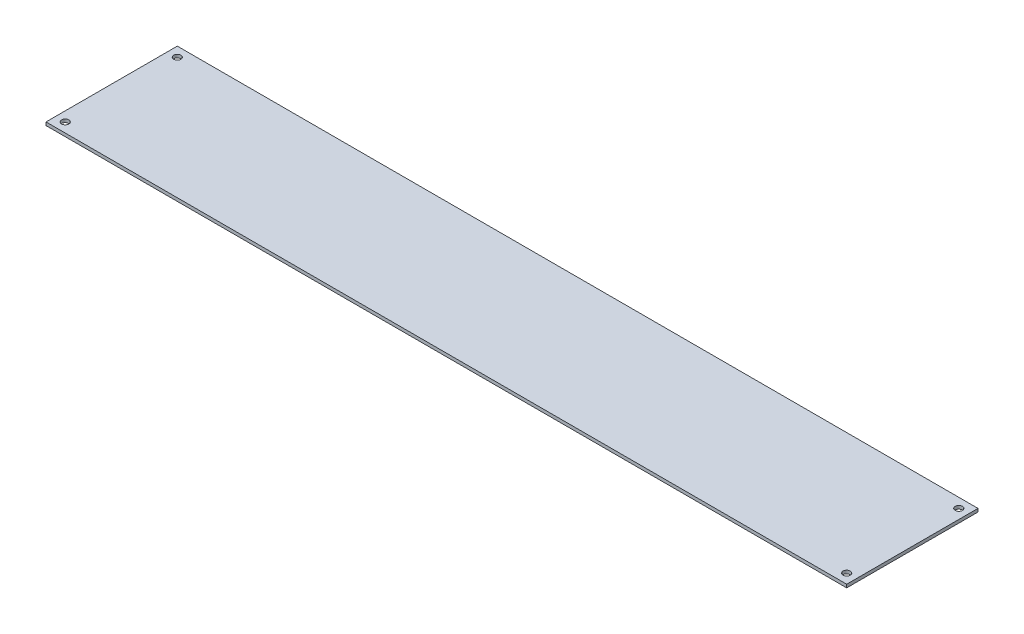
SolidWorks part; units mm, degrees
ref_plane "Front Plane" through (0, 0, 0) normal (0, 0, 1) x (1, 0, 0)
ref_plane "Top Plane" through (0, 0, 0) normal (0, 1, 0) x (1, 0, 0)
ref_plane "Right Plane" through (0, 0, 0) normal (1, 0, 0) x (0, 0, -1)
sketch "Sketch1" plane through (0, 0, 0) normal (0, 1, 0) x (1, 0, 0)
  line L1 (0, 0) -> (500, 0)
  line L2 (0, 0) -> (0, 82)
  line L3 (0, 82) -> (500, 82)
  line L4 (500, 0) -> (500, 82)
  dimension "D1" = 500
  dimension "D2" = 82
extrude "Boss-Extrude1" add sketch "Sketch1" along normal blind 2
hole_wizard "M4 Clearance Hole1" positions "Sketch3" profile "Sketch4" hole size "M4" standard "DIN" end condition up to next
sketch "Sketch3" plane through (0, 0, 0) normal (0, -1, 0) x (-1, 0, 0)
  line L0 (-500, 82) -> (0, 82) construction
  line L1 (0, 82) -> (0, 0) construction
  line L2 (-500, 0) -> (-500, 82) construction
  line L3 (0, 0) -> (-500, 0) construction
  point P0 (-6, 6)
  point P2 (-6, 76)
  point P4 (-494, 76)
  point P6 (-494, 6)
  dimension "D1" = 6
  dimension "D2" = 6
  dimension "D3" = 6
  dimension "D4" = 6
sketch "Sketch4" plane through (6, 0, -6) normal (1, 0, 0) x (0, 0, -1)
  line L0 (0, 0) -> (0, 2)
  line L1 (0, 2) -> (2.25, 2)
  line L2 (2.25, 2) -> (2.25, 0)
  line L5 (2.25, 0) -> (0, 0)
  line L11 (0, -6.35) -> (0, 107.95) construction
  dimension "Thru Hole Dia." = 4.5
  dimension "Thru Hole Depth" = 2
sketch "Sketch5" plane through (0, 0, 0) normal (0, -1, 0) x (1, 0, 0)
  line L0 (0, -82) -> (0, 0) construction
  line L1 (500, -82) -> (0, -82) construction
  line L189 (0, 0) -> (500, 0) construction
  line L190 (26.3868, -5) -> (24.9434, -2.5)
  line L191 (24.9434, -2.5) -> (22.0566, -2.5)
  line L192 (22.0566, -2.5) -> (20.6132, -5)
  line L193 (20.6132, -5) -> (22.0566, -7.5)
  line L194 (22.0566, -7.5) -> (24.9434, -7.5)
  line L195 (24.9434, -7.5) -> (26.3868, -5)
  line L196 (36.3868, -5) -> (34.9434, -2.5)
  line L197 (34.9434, -2.5) -> (32.0566, -2.5)
  line L198 (32.0566, -2.5) -> (30.6132, -5)
  line L199 (30.6132, -5) -> (32.0566, -7.5)
  line L200 (32.0566, -7.5) -> (34.9434, -7.5)
  line L201 (34.9434, -7.5) -> (36.3868, -5)
  line L202 (46.3868, -5) -> (44.9434, -2.5)
  line L203 (44.9434, -2.5) -> (42.0566, -2.5)
  line L204 (42.0566, -2.5) -> (40.6132, -5)
  line L205 (40.6132, -5) -> (42.0566, -7.5)
  line L206 (42.0566, -7.5) -> (44.9434, -7.5)
  line L207 (44.9434, -7.5) -> (46.3868, -5)
  line L208 (56.3868, -5) -> (54.9434, -2.5)
  line L209 (54.9434, -2.5) -> (52.0566, -2.5)
  line L210 (52.0566, -2.5) -> (50.6132, -5)
  line L211 (50.6132, -5) -> (52.0566, -7.5)
  line L212 (52.0566, -7.5) -> (54.9434, -7.5)
  line L213 (54.9434, -7.5) -> (56.3868, -5)
  line L214 (66.3868, -5) -> (64.9434, -2.5)
  line L215 (64.9434, -2.5) -> (62.0566, -2.5)
  line L216 (62.0566, -2.5) -> (60.6132, -5)
  line L217 (60.6132, -5) -> (62.0566, -7.5)
  line L218 (62.0566, -7.5) -> (64.9434, -7.5)
  line L219 (64.9434, -7.5) -> (66.3868, -5)
  line L220 (76.3868, -5) -> (74.9434, -2.5)
  line L221 (74.9434, -2.5) -> (72.0566, -2.5)
  line L222 (72.0566, -2.5) -> (70.6132, -5)
  line L223 (70.6132, -5) -> (72.0566, -7.5)
  line L224 (72.0566, -7.5) -> (74.9434, -7.5)
  line L225 (74.9434, -7.5) -> (76.3868, -5)
  line L226 (86.3868, -5) -> (84.9434, -2.5)
  line L227 (84.9434, -2.5) -> (82.0566, -2.5)
  line L228 (82.0566, -2.5) -> (80.6132, -5)
  line L229 (80.6132, -5) -> (82.0566, -7.5)
  line L230 (82.0566, -7.5) -> (84.9434, -7.5)
  line L231 (84.9434, -7.5) -> (86.3868, -5)
  line L232 (96.3868, -5) -> (94.9434, -2.5)
  line L233 (94.9434, -2.5) -> (92.0566, -2.5)
  line L234 (92.0566, -2.5) -> (90.6132, -5)
  line L235 (90.6132, -5) -> (92.0566, -7.5)
  line L236 (92.0566, -7.5) -> (94.9434, -7.5)
  line L237 (94.9434, -7.5) -> (96.3868, -5)
  line L238 (106.3868, -5) -> (104.9434, -2.5)
  line L239 (104.9434, -2.5) -> (102.0566, -2.5)
  line L240 (102.0566, -2.5) -> (100.6132, -5)
  line L241 (100.6132, -5) -> (102.0566, -7.5)
  line L242 (102.0566, -7.5) -> (104.9434, -7.5)
  line L243 (104.9434, -7.5) -> (106.3868, -5)
  line L244 (116.3868, -5) -> (114.9434, -2.5)
  line L245 (114.9434, -2.5) -> (112.0566, -2.5)
  line L246 (112.0566, -2.5) -> (110.6132, -5)
  line L247 (110.6132, -5) -> (112.0566, -7.5)
  line L248 (112.0566, -7.5) -> (114.9434, -7.5)
  line L249 (114.9434, -7.5) -> (116.3868, -5)
  line L250 (126.3868, -5) -> (124.9434, -2.5)
  line L251 (124.9434, -2.5) -> (122.0566, -2.5)
  line L252 (122.0566, -2.5) -> (120.6132, -5)
  line L253 (120.6132, -5) -> (122.0566, -7.5)
  line L254 (122.0566, -7.5) -> (124.9434, -7.5)
  line L255 (124.9434, -7.5) -> (126.3868, -5)
  line L256 (136.3868, -5) -> (134.9434, -2.5)
  line L257 (134.9434, -2.5) -> (132.0566, -2.5)
  line L258 (132.0566, -2.5) -> (130.6132, -5)
  line L259 (130.6132, -5) -> (132.0566, -7.5)
  line L260 (132.0566, -7.5) -> (134.9434, -7.5)
  line L261 (134.9434, -7.5) -> (136.3868, -5)
  line L262 (146.3868, -5) -> (144.9434, -2.5)
  line L263 (144.9434, -2.5) -> (142.0566, -2.5)
  line L264 (142.0566, -2.5) -> (140.6132, -5)
  line L265 (140.6132, -5) -> (142.0566, -7.5)
  line L266 (142.0566, -7.5) -> (144.9434, -7.5)
  line L267 (144.9434, -7.5) -> (146.3868, -5)
  line L268 (36.3868, -15) -> (34.9434, -12.5)
  line L269 (34.9434, -12.5) -> (32.0566, -12.5)
  line L270 (32.0566, -12.5) -> (30.6132, -15)
  line L271 (30.6132, -15) -> (32.0566, -17.5)
  line L272 (32.0566, -17.5) -> (34.9434, -17.5)
  line L273 (34.9434, -17.5) -> (36.3868, -15)
  line L274 (46.3868, -15) -> (44.9434, -12.5)
  line L275 (44.9434, -12.5) -> (42.0566, -12.5)
  line L276 (42.0566, -12.5) -> (40.6132, -15)
  line L277 (40.6132, -15) -> (42.0566, -17.5)
  line L278 (42.0566, -17.5) -> (44.9434, -17.5)
  line L279 (44.9434, -17.5) -> (46.3868, -15)
  line L280 (56.3868, -15) -> (54.9434, -12.5)
  line L281 (54.9434, -12.5) -> (52.0566, -12.5)
  line L282 (52.0566, -12.5) -> (50.6132, -15)
  line L283 (50.6132, -15) -> (52.0566, -17.5)
  line L284 (52.0566, -17.5) -> (54.9434, -17.5)
  line L285 (54.9434, -17.5) -> (56.3868, -15)
  line L286 (66.3868, -15) -> (64.9434, -12.5)
  line L287 (64.9434, -12.5) -> (62.0566, -12.5)
  line L288 (62.0566, -12.5) -> (60.6132, -15)
  line L289 (60.6132, -15) -> (62.0566, -17.5)
  line L290 (62.0566, -17.5) -> (64.9434, -17.5)
  line L291 (64.9434, -17.5) -> (66.3868, -15)
  line L292 (76.3868, -15) -> (74.9434, -12.5)
  line L293 (74.9434, -12.5) -> (72.0566, -12.5)
  line L294 (72.0566, -12.5) -> (70.6132, -15)
  line L295 (70.6132, -15) -> (72.0566, -17.5)
  line L296 (72.0566, -17.5) -> (74.9434, -17.5)
  line L297 (74.9434, -17.5) -> (76.3868, -15)
  line L298 (86.3868, -15) -> (84.9434, -12.5)
  line L299 (84.9434, -12.5) -> (82.0566, -12.5)
  line L300 (82.0566, -12.5) -> (80.6132, -15)
  line L301 (80.6132, -15) -> (82.0566, -17.5)
  line L302 (82.0566, -17.5) -> (84.9434, -17.5)
  line L303 (84.9434, -17.5) -> (86.3868, -15)
  line L304 (96.3868, -15) -> (94.9434, -12.5)
  line L305 (94.9434, -12.5) -> (92.0566, -12.5)
  line L306 (92.0566, -12.5) -> (90.6132, -15)
  line L307 (90.6132, -15) -> (92.0566, -17.5)
  line L308 (92.0566, -17.5) -> (94.9434, -17.5)
  line L309 (94.9434, -17.5) -> (96.3868, -15)
  line L310 (106.3868, -15) -> (104.9434, -12.5)
  line L311 (104.9434, -12.5) -> (102.0566, -12.5)
  line L312 (102.0566, -12.5) -> (100.6132, -15)
  line L313 (100.6132, -15) -> (102.0566, -17.5)
  line L314 (102.0566, -17.5) -> (104.9434, -17.5)
  line L315 (104.9434, -17.5) -> (106.3868, -15)
  line L316 (116.3868, -15) -> (114.9434, -12.5)
  line L317 (114.9434, -12.5) -> (112.0566, -12.5)
  line L318 (112.0566, -12.5) -> (110.6132, -15)
  line L319 (110.6132, -15) -> (112.0566, -17.5)
  line L320 (112.0566, -17.5) -> (114.9434, -17.5)
  line L321 (114.9434, -17.5) -> (116.3868, -15)
  line L322 (126.3868, -15) -> (124.9434, -12.5)
  line L323 (124.9434, -12.5) -> (122.0566, -12.5)
  line L324 (122.0566, -12.5) -> (120.6132, -15)
  line L325 (120.6132, -15) -> (122.0566, -17.5)
  line L326 (122.0566, -17.5) -> (124.9434, -17.5)
  line L327 (124.9434, -17.5) -> (126.3868, -15)
  line L328 (136.3868, -15) -> (134.9434, -12.5)
  line L329 (134.9434, -12.5) -> (132.0566, -12.5)
  line L330 (132.0566, -12.5) -> (130.6132, -15)
  line L331 (130.6132, -15) -> (132.0566, -17.5)
  line L332 (132.0566, -17.5) -> (134.9434, -17.5)
  line L333 (134.9434, -17.5) -> (136.3868, -15)
  line L334 (146.3868, -15) -> (144.9434, -12.5)
  line L335 (144.9434, -12.5) -> (142.0566, -12.5)
  line L336 (142.0566, -12.5) -> (140.6132, -15)
  line L337 (140.6132, -15) -> (142.0566, -17.5)
  line L338 (142.0566, -17.5) -> (144.9434, -17.5)
  line L339 (144.9434, -17.5) -> (146.3868, -15)
  line L340 (36.3868, -25) -> (34.9434, -22.5)
  line L341 (34.9434, -22.5) -> (32.0566, -22.5)
  line L342 (32.0566, -22.5) -> (30.6132, -25)
  line L343 (30.6132, -25) -> (32.0566, -27.5)
  line L344 (32.0566, -27.5) -> (34.9434, -27.5)
  line L345 (34.9434, -27.5) -> (36.3868, -25)
  line L346 (46.3868, -25) -> (44.9434, -22.5)
  line L347 (44.9434, -22.5) -> (42.0566, -22.5)
  line L348 (42.0566, -22.5) -> (40.6132, -25)
  line L349 (40.6132, -25) -> (42.0566, -27.5)
  line L350 (42.0566, -27.5) -> (44.9434, -27.5)
  line L351 (44.9434, -27.5) -> (46.3868, -25)
  line L352 (56.3868, -25) -> (54.9434, -22.5)
  line L353 (54.9434, -22.5) -> (52.0566, -22.5)
  line L354 (52.0566, -22.5) -> (50.6132, -25)
  line L355 (50.6132, -25) -> (52.0566, -27.5)
  line L356 (52.0566, -27.5) -> (54.9434, -27.5)
  line L357 (54.9434, -27.5) -> (56.3868, -25)
  line L358 (66.3868, -25) -> (64.9434, -22.5)
  line L359 (64.9434, -22.5) -> (62.0566, -22.5)
  line L360 (62.0566, -22.5) -> (60.6132, -25)
  line L361 (60.6132, -25) -> (62.0566, -27.5)
  line L362 (62.0566, -27.5) -> (64.9434, -27.5)
  line L363 (64.9434, -27.5) -> (66.3868, -25)
  line L364 (76.3868, -25) -> (74.9434, -22.5)
  line L365 (74.9434, -22.5) -> (72.0566, -22.5)
  line L366 (72.0566, -22.5) -> (70.6132, -25)
  line L367 (70.6132, -25) -> (72.0566, -27.5)
  line L368 (72.0566, -27.5) -> (74.9434, -27.5)
  line L369 (74.9434, -27.5) -> (76.3868, -25)
  line L370 (86.3868, -25) -> (84.9434, -22.5)
  line L371 (84.9434, -22.5) -> (82.0566, -22.5)
  line L372 (82.0566, -22.5) -> (80.6132, -25)
  line L373 (80.6132, -25) -> (82.0566, -27.5)
  line L374 (82.0566, -27.5) -> (84.9434, -27.5)
  line L375 (84.9434, -27.5) -> (86.3868, -25)
  line L376 (96.3868, -25) -> (94.9434, -22.5)
  line L377 (94.9434, -22.5) -> (92.0566, -22.5)
  line L378 (92.0566, -22.5) -> (90.6132, -25)
  line L379 (90.6132, -25) -> (92.0566, -27.5)
  line L380 (92.0566, -27.5) -> (94.9434, -27.5)
  line L381 (94.9434, -27.5) -> (96.3868, -25)
  line L382 (106.3868, -25) -> (104.9434, -22.5)
  line L383 (104.9434, -22.5) -> (102.0566, -22.5)
  line L384 (102.0566, -22.5) -> (100.6132, -25)
  line L385 (100.6132, -25) -> (102.0566, -27.5)
  line L386 (102.0566, -27.5) -> (104.9434, -27.5)
  line L387 (104.9434, -27.5) -> (106.3868, -25)
  line L388 (116.3868, -25) -> (114.9434, -22.5)
  line L389 (114.9434, -22.5) -> (112.0566, -22.5)
  line L390 (112.0566, -22.5) -> (110.6132, -25)
  line L391 (110.6132, -25) -> (112.0566, -27.5)
  line L392 (112.0566, -27.5) -> (114.9434, -27.5)
  line L393 (114.9434, -27.5) -> (116.3868, -25)
  line L394 (126.3868, -25) -> (124.9434, -22.5)
  line L395 (124.9434, -22.5) -> (122.0566, -22.5)
  line L396 (122.0566, -22.5) -> (120.6132, -25)
  line L397 (120.6132, -25) -> (122.0566, -27.5)
  line L398 (122.0566, -27.5) -> (124.9434, -27.5)
  line L399 (124.9434, -27.5) -> (126.3868, -25)
  line L400 (136.3868, -25) -> (134.9434, -22.5)
  line L401 (134.9434, -22.5) -> (132.0566, -22.5)
  line L402 (132.0566, -22.5) -> (130.6132, -25)
  line L403 (130.6132, -25) -> (132.0566, -27.5)
  line L404 (132.0566, -27.5) -> (134.9434, -27.5)
  line L405 (134.9434, -27.5) -> (136.3868, -25)
  line L412 (36.3868, -35) -> (34.9434, -32.5)
  line L413 (34.9434, -32.5) -> (32.0566, -32.5)
  line L414 (32.0566, -32.5) -> (30.6132, -35)
  line L415 (30.6132, -35) -> (32.0566, -37.5)
  line L416 (32.0566, -37.5) -> (34.9434, -37.5)
  line L417 (34.9434, -37.5) -> (36.3868, -35)
  line L418 (46.3868, -35) -> (44.9434, -32.5)
  line L419 (44.9434, -32.5) -> (42.0566, -32.5)
  line L420 (42.0566, -32.5) -> (40.6132, -35)
  line L421 (40.6132, -35) -> (42.0566, -37.5)
  line L422 (42.0566, -37.5) -> (44.9434, -37.5)
  line L423 (44.9434, -37.5) -> (46.3868, -35)
  line L424 (56.3868, -35) -> (54.9434, -32.5)
  line L425 (54.9434, -32.5) -> (52.0566, -32.5)
  line L426 (52.0566, -32.5) -> (50.6132, -35)
  line L427 (50.6132, -35) -> (52.0566, -37.5)
  line L428 (52.0566, -37.5) -> (54.9434, -37.5)
  line L429 (54.9434, -37.5) -> (56.3868, -35)
  line L430 (66.3868, -35) -> (64.9434, -32.5)
  line L431 (64.9434, -32.5) -> (62.0566, -32.5)
  line L432 (62.0566, -32.5) -> (60.6132, -35)
  line L433 (60.6132, -35) -> (62.0566, -37.5)
  line L434 (62.0566, -37.5) -> (64.9434, -37.5)
  line L435 (64.9434, -37.5) -> (66.3868, -35)
  line L436 (76.3868, -35) -> (74.9434, -32.5)
  line L437 (74.9434, -32.5) -> (72.0566, -32.5)
  line L438 (72.0566, -32.5) -> (70.6132, -35)
  line L439 (70.6132, -35) -> (72.0566, -37.5)
  line L440 (72.0566, -37.5) -> (74.9434, -37.5)
  line L441 (74.9434, -37.5) -> (76.3868, -35)
  line L442 (86.3868, -35) -> (84.9434, -32.5)
  line L443 (84.9434, -32.5) -> (82.0566, -32.5)
  line L444 (82.0566, -32.5) -> (80.6132, -35)
  line L445 (80.6132, -35) -> (82.0566, -37.5)
  line L446 (82.0566, -37.5) -> (84.9434, -37.5)
  line L447 (84.9434, -37.5) -> (86.3868, -35)
  line L448 (96.3868, -35) -> (94.9434, -32.5)
  line L449 (94.9434, -32.5) -> (92.0566, -32.5)
  line L450 (92.0566, -32.5) -> (90.6132, -35)
  line L451 (90.6132, -35) -> (92.0566, -37.5)
  line L452 (92.0566, -37.5) -> (94.9434, -37.5)
  line L453 (94.9434, -37.5) -> (96.3868, -35)
  line L454 (106.3868, -35) -> (104.9434, -32.5)
  line L455 (104.9434, -32.5) -> (102.0566, -32.5)
  line L456 (102.0566, -32.5) -> (100.6132, -35)
  line L457 (100.6132, -35) -> (102.0566, -37.5)
  line L458 (102.0566, -37.5) -> (104.9434, -37.5)
  line L459 (104.9434, -37.5) -> (106.3868, -35)
  line L460 (116.3868, -35) -> (114.9434, -32.5)
  line L461 (114.9434, -32.5) -> (112.0566, -32.5)
  line L462 (112.0566, -32.5) -> (110.6132, -35)
  line L463 (110.6132, -35) -> (112.0566, -37.5)
  line L464 (112.0566, -37.5) -> (114.9434, -37.5)
  line L465 (114.9434, -37.5) -> (116.3868, -35)
  line L466 (126.3868, -35) -> (124.9434, -32.5)
  line L467 (124.9434, -32.5) -> (122.0566, -32.5)
  line L468 (122.0566, -32.5) -> (120.6132, -35)
  line L469 (120.6132, -35) -> (122.0566, -37.5)
  line L470 (122.0566, -37.5) -> (124.9434, -37.5)
  line L471 (124.9434, -37.5) -> (126.3868, -35)
  line L472 (136.3868, -35) -> (134.9434, -32.5)
  line L473 (134.9434, -32.5) -> (132.0566, -32.5)
  line L474 (132.0566, -32.5) -> (130.6132, -35)
  line L475 (130.6132, -35) -> (132.0566, -37.5)
  line L476 (132.0566, -37.5) -> (134.9434, -37.5)
  line L477 (134.9434, -37.5) -> (136.3868, -35)
  line L490 (46.3868, -45) -> (44.9434, -42.5)
  line L491 (44.9434, -42.5) -> (42.0566, -42.5)
  line L492 (42.0566, -42.5) -> (40.6132, -45)
  line L493 (40.6132, -45) -> (42.0566, -47.5)
  line L494 (42.0566, -47.5) -> (44.9434, -47.5)
  line L495 (44.9434, -47.5) -> (46.3868, -45)
  line L496 (56.3868, -45) -> (54.9434, -42.5)
  line L497 (54.9434, -42.5) -> (52.0566, -42.5)
  line L498 (52.0566, -42.5) -> (50.6132, -45)
  line L499 (50.6132, -45) -> (52.0566, -47.5)
  line L500 (52.0566, -47.5) -> (54.9434, -47.5)
  line L501 (54.9434, -47.5) -> (56.3868, -45)
  line L502 (66.3868, -45) -> (64.9434, -42.5)
  line L503 (64.9434, -42.5) -> (62.0566, -42.5)
  line L504 (62.0566, -42.5) -> (60.6132, -45)
  line L505 (60.6132, -45) -> (62.0566, -47.5)
  line L506 (62.0566, -47.5) -> (64.9434, -47.5)
  line L507 (64.9434, -47.5) -> (66.3868, -45)
  line L508 (76.3868, -45) -> (74.9434, -42.5)
  line L509 (74.9434, -42.5) -> (72.0566, -42.5)
  line L510 (72.0566, -42.5) -> (70.6132, -45)
  line L511 (70.6132, -45) -> (72.0566, -47.5)
  line L512 (72.0566, -47.5) -> (74.9434, -47.5)
  line L513 (74.9434, -47.5) -> (76.3868, -45)
  line L514 (86.3868, -45) -> (84.9434, -42.5)
  line L515 (84.9434, -42.5) -> (82.0566, -42.5)
  line L516 (82.0566, -42.5) -> (80.6132, -45)
  line L517 (80.6132, -45) -> (82.0566, -47.5)
  line L518 (82.0566, -47.5) -> (84.9434, -47.5)
  line L519 (84.9434, -47.5) -> (86.3868, -45)
  line L520 (96.3868, -45) -> (94.9434, -42.5)
  line L521 (94.9434, -42.5) -> (92.0566, -42.5)
  line L522 (92.0566, -42.5) -> (90.6132, -45)
  line L523 (90.6132, -45) -> (92.0566, -47.5)
  line L524 (92.0566, -47.5) -> (94.9434, -47.5)
  line L525 (94.9434, -47.5) -> (96.3868, -45)
  line L526 (106.3868, -45) -> (104.9434, -42.5)
  line L527 (104.9434, -42.5) -> (102.0566, -42.5)
  line L528 (102.0566, -42.5) -> (100.6132, -45)
  line L529 (100.6132, -45) -> (102.0566, -47.5)
  line L530 (102.0566, -47.5) -> (104.9434, -47.5)
  line L531 (104.9434, -47.5) -> (106.3868, -45)
  line L532 (116.3868, -45) -> (114.9434, -42.5)
  line L533 (114.9434, -42.5) -> (112.0566, -42.5)
  line L534 (112.0566, -42.5) -> (110.6132, -45)
  line L535 (110.6132, -45) -> (112.0566, -47.5)
  line L536 (112.0566, -47.5) -> (114.9434, -47.5)
  line L537 (114.9434, -47.5) -> (116.3868, -45)
  line L538 (126.3868, -45) -> (124.9434, -42.5)
  line L539 (124.9434, -42.5) -> (122.0566, -42.5)
  line L540 (122.0566, -42.5) -> (120.6132, -45)
  line L541 (120.6132, -45) -> (122.0566, -47.5)
  line L542 (122.0566, -47.5) -> (124.9434, -47.5)
  line L543 (124.9434, -47.5) -> (126.3868, -45)
  line L568 (56.3868, -55) -> (54.9434, -52.5)
  line L569 (54.9434, -52.5) -> (52.0566, -52.5)
  line L570 (52.0566, -52.5) -> (50.6132, -55)
  line L571 (50.6132, -55) -> (52.0566, -57.5)
  line L572 (52.0566, -57.5) -> (54.9434, -57.5)
  line L573 (54.9434, -57.5) -> (56.3868, -55)
  line L574 (66.3868, -55) -> (64.9434, -52.5)
  line L575 (64.9434, -52.5) -> (62.0566, -52.5)
  line L576 (62.0566, -52.5) -> (60.6132, -55)
  line L577 (60.6132, -55) -> (62.0566, -57.5)
  line L578 (62.0566, -57.5) -> (64.9434, -57.5)
  line L579 (64.9434, -57.5) -> (66.3868, -55)
  line L580 (76.3868, -55) -> (74.9434, -52.5)
  line L581 (74.9434, -52.5) -> (72.0566, -52.5)
  line L582 (72.0566, -52.5) -> (70.6132, -55)
  line L583 (70.6132, -55) -> (72.0566, -57.5)
  line L584 (72.0566, -57.5) -> (74.9434, -57.5)
  line L585 (74.9434, -57.5) -> (76.3868, -55)
  line L586 (86.3868, -55) -> (84.9434, -52.5)
  line L587 (84.9434, -52.5) -> (82.0566, -52.5)
  line L588 (82.0566, -52.5) -> (80.6132, -55)
  line L589 (80.6132, -55) -> (82.0566, -57.5)
  line L590 (82.0566, -57.5) -> (84.9434, -57.5)
  line L591 (84.9434, -57.5) -> (86.3868, -55)
  line L592 (96.3868, -55) -> (94.9434, -52.5)
  line L593 (94.9434, -52.5) -> (92.0566, -52.5)
  line L594 (92.0566, -52.5) -> (90.6132, -55)
  line L595 (90.6132, -55) -> (92.0566, -57.5)
  line L596 (92.0566, -57.5) -> (94.9434, -57.5)
  line L597 (94.9434, -57.5) -> (96.3868, -55)
  line L598 (106.3868, -55) -> (104.9434, -52.5)
  line L599 (104.9434, -52.5) -> (102.0566, -52.5)
  line L600 (102.0566, -52.5) -> (100.6132, -55)
  line L601 (100.6132, -55) -> (102.0566, -57.5)
  line L602 (102.0566, -57.5) -> (104.9434, -57.5)
  line L603 (104.9434, -57.5) -> (106.3868, -55)
  line L604 (116.3868, -55) -> (114.9434, -52.5)
  line L605 (114.9434, -52.5) -> (112.0566, -52.5)
  line L606 (112.0566, -52.5) -> (110.6132, -55)
  line L607 (110.6132, -55) -> (112.0566, -57.5)
  line L608 (112.0566, -57.5) -> (114.9434, -57.5)
  line L609 (114.9434, -57.5) -> (116.3868, -55)
  line L652 (76.3868, -65) -> (74.9434, -62.5)
  line L653 (74.9434, -62.5) -> (72.0566, -62.5)
  line L654 (72.0566, -62.5) -> (70.6132, -65)
  line L655 (70.6132, -65) -> (72.0566, -67.5)
  line L656 (72.0566, -67.5) -> (74.9434, -67.5)
  line L657 (74.9434, -67.5) -> (76.3868, -65)
  line L658 (86.3868, -65) -> (84.9434, -62.5)
  line L659 (84.9434, -62.5) -> (82.0566, -62.5)
  line L660 (82.0566, -62.5) -> (80.6132, -65)
  line L661 (80.6132, -65) -> (82.0566, -67.5)
  line L662 (82.0566, -67.5) -> (84.9434, -67.5)
  line L663 (84.9434, -67.5) -> (86.3868, -65)
  line L664 (96.3868, -65) -> (94.9434, -62.5)
  line L665 (94.9434, -62.5) -> (92.0566, -62.5)
  line L666 (92.0566, -62.5) -> (90.6132, -65)
  line L667 (90.6132, -65) -> (92.0566, -67.5)
  line L668 (92.0566, -67.5) -> (94.9434, -67.5)
  line L669 (94.9434, -67.5) -> (96.3868, -65)
  line L700 (26.3868, -15) -> (24.9434, -12.5)
  line L701 (24.9434, -12.5) -> (22.0566, -12.5)
  line L702 (22.0566, -12.5) -> (20.6132, -15)
  line L703 (20.6132, -15) -> (22.0566, -17.5)
  line L704 (22.0566, -17.5) -> (24.9434, -17.5)
  line L705 (24.9434, -17.5) -> (26.3868, -15)
  line L736 (146.3868, -65) -> (144.9434, -62.5) [skipped]
  line L737 (144.9434, -62.5) -> (142.0566, -62.5) [skipped]
  line L738 (142.0566, -62.5) -> (140.6132, -65) [skipped]
  line L739 (140.6132, -65) -> (142.0566, -67.5) [skipped]
  line L740 (142.0566, -67.5) -> (144.9434, -67.5) [skipped]
  line L741 (144.9434, -67.5) -> (146.3868, -65) [skipped]
  line L742 (136.3868, -65) -> (134.9434, -62.5) [skipped]
  line L743 (134.9434, -62.5) -> (132.0566, -62.5) [skipped]
  line L744 (132.0566, -62.5) -> (130.6132, -65) [skipped]
  line L745 (130.6132, -65) -> (132.0566, -67.5) [skipped]
  line L746 (132.0566, -67.5) -> (134.9434, -67.5) [skipped]
  line L747 (134.9434, -67.5) -> (136.3868, -65) [skipped]
  line L748 (126.3868, -65) -> (124.9434, -62.5) [skipped]
  line L749 (124.9434, -62.5) -> (122.0566, -62.5) [skipped]
  line L750 (122.0566, -62.5) -> (120.6132, -65) [skipped]
  line L751 (120.6132, -65) -> (122.0566, -67.5) [skipped]
  line L752 (122.0566, -67.5) -> (124.9434, -67.5) [skipped]
  line L753 (124.9434, -67.5) -> (126.3868, -65) [skipped]
  line L754 (116.3868, -65) -> (114.9434, -62.5) [skipped]
  line L755 (114.9434, -62.5) -> (112.0566, -62.5) [skipped]
  line L756 (112.0566, -62.5) -> (110.6132, -65) [skipped]
  line L757 (110.6132, -65) -> (112.0566, -67.5) [skipped]
  line L758 (112.0566, -67.5) -> (114.9434, -67.5) [skipped]
  line L759 (114.9434, -67.5) -> (116.3868, -65) [skipped]
  line L760 (106.3868, -65) -> (104.9434, -62.5) [skipped]
  line L761 (104.9434, -62.5) -> (102.0566, -62.5) [skipped]
  line L762 (102.0566, -62.5) -> (100.6132, -65) [skipped]
  line L763 (100.6132, -65) -> (102.0566, -67.5) [skipped]
  line L764 (102.0566, -67.5) -> (104.9434, -67.5) [skipped]
  line L765 (104.9434, -67.5) -> (106.3868, -65) [skipped]
  line L766 (126.3868, -55) -> (124.9434, -52.5) [skipped]
  line L767 (124.9434, -52.5) -> (122.0566, -52.5) [skipped]
  line L768 (122.0566, -52.5) -> (120.6132, -55) [skipped]
  line L769 (120.6132, -55) -> (122.0566, -57.5) [skipped]
  line L770 (122.0566, -57.5) -> (124.9434, -57.5) [skipped]
  line L771 (124.9434, -57.5) -> (126.3868, -55) [skipped]
  line L772 (136.3868, -55) -> (134.9434, -52.5) [skipped]
  line L773 (134.9434, -52.5) -> (132.0566, -52.5) [skipped]
  line L774 (132.0566, -52.5) -> (130.6132, -55) [skipped]
  line L775 (130.6132, -55) -> (132.0566, -57.5) [skipped]
  line L776 (132.0566, -57.5) -> (134.9434, -57.5) [skipped]
  line L777 (134.9434, -57.5) -> (136.3868, -55) [skipped]
  line L778 (146.3868, -55) -> (144.9434, -52.5) [skipped]
  line L779 (144.9434, -52.5) -> (142.0566, -52.5) [skipped]
  line L780 (142.0566, -52.5) -> (140.6132, -55) [skipped]
  line L781 (140.6132, -55) -> (142.0566, -57.5) [skipped]
  line L782 (142.0566, -57.5) -> (144.9434, -57.5) [skipped]
  line L783 (144.9434, -57.5) -> (146.3868, -55) [skipped]
  line L784 (146.3868, -45) -> (144.9434, -42.5) [skipped]
  line L785 (144.9434, -42.5) -> (142.0566, -42.5) [skipped]
  line L786 (142.0566, -42.5) -> (140.6132, -45) [skipped]
  line L787 (140.6132, -45) -> (142.0566, -47.5) [skipped]
  line L788 (142.0566, -47.5) -> (144.9434, -47.5) [skipped]
  line L789 (144.9434, -47.5) -> (146.3868, -45) [skipped]
  line L790 (136.3868, -45) -> (134.9434, -42.5) [skipped]
  line L791 (134.9434, -42.5) -> (132.0566, -42.5) [skipped]
  line L792 (132.0566, -42.5) -> (130.6132, -45) [skipped]
  line L793 (130.6132, -45) -> (132.0566, -47.5) [skipped]
  line L794 (132.0566, -47.5) -> (134.9434, -47.5) [skipped]
  line L795 (134.9434, -47.5) -> (136.3868, -45) [skipped]
  line L796 (146.3868, -35) -> (144.9434, -32.5) [skipped]
  line L797 (144.9434, -32.5) -> (142.0566, -32.5) [skipped]
  line L798 (142.0566, -32.5) -> (140.6132, -35) [skipped]
  line L799 (140.6132, -35) -> (142.0566, -37.5) [skipped]
  line L800 (142.0566, -37.5) -> (144.9434, -37.5) [skipped]
  line L801 (144.9434, -37.5) -> (146.3868, -35) [skipped]
  line L802 (146.3868, -25) -> (144.9434, -22.5) [skipped]
  line L803 (144.9434, -22.5) -> (142.0566, -22.5) [skipped]
  line L804 (142.0566, -22.5) -> (140.6132, -25) [skipped]
  line L805 (140.6132, -25) -> (142.0566, -27.5) [skipped]
  line L806 (142.0566, -27.5) -> (144.9434, -27.5) [skipped]
  line L807 (144.9434, -27.5) -> (146.3868, -25) [skipped]
  line L808 (26.3868, -25) -> (24.9434, -22.5) [skipped]
  line L809 (24.9434, -22.5) -> (22.0566, -22.5) [skipped]
  line L810 (22.0566, -22.5) -> (20.6132, -25) [skipped]
  line L811 (20.6132, -25) -> (22.0566, -27.5) [skipped]
  line L812 (22.0566, -27.5) -> (24.9434, -27.5) [skipped]
  line L813 (24.9434, -27.5) -> (26.3868, -25) [skipped]
  line L814 (26.3868, -35) -> (24.9434, -32.5) [skipped]
  line L815 (24.9434, -32.5) -> (22.0566, -32.5) [skipped]
  line L816 (22.0566, -32.5) -> (20.6132, -35) [skipped]
  line L817 (20.6132, -35) -> (22.0566, -37.5) [skipped]
  line L818 (22.0566, -37.5) -> (24.9434, -37.5) [skipped]
  line L819 (24.9434, -37.5) -> (26.3868, -35) [skipped]
  line L820 (26.3868, -45) -> (24.9434, -42.5) [skipped]
  line L821 (24.9434, -42.5) -> (22.0566, -42.5) [skipped]
  line L822 (22.0566, -42.5) -> (20.6132, -45) [skipped]
  line L823 (20.6132, -45) -> (22.0566, -47.5) [skipped]
  line L824 (22.0566, -47.5) -> (24.9434, -47.5) [skipped]
  line L825 (24.9434, -47.5) -> (26.3868, -45) [skipped]
  line L826 (22.0566, -52.5) -> (20.6132, -55) [skipped]
  line L827 (26.3868, -55) -> (24.9434, -52.5) [skipped]
  line L828 (24.9434, -52.5) -> (22.0566, -52.5) [skipped]
  line L829 (20.6132, -55) -> (22.0566, -57.5) [skipped]
  line L830 (22.0566, -57.5) -> (24.9434, -57.5) [skipped]
  line L831 (24.9434, -57.5) -> (26.3868, -55) [skipped]
  line L832 (26.3868, -65) -> (24.9434, -62.5) [skipped]
  line L833 (24.9434, -62.5) -> (22.0566, -62.5) [skipped]
  line L834 (22.0566, -62.5) -> (20.6132, -65) [skipped]
  line L835 (20.6132, -65) -> (22.0566, -67.5) [skipped]
  line L836 (22.0566, -67.5) -> (24.9434, -67.5) [skipped]
  line L837 (24.9434, -67.5) -> (26.3868, -65) [skipped]
  line L838 (36.3868, -55) -> (34.9434, -52.5) [skipped]
  line L839 (34.9434, -52.5) -> (32.0566, -52.5) [skipped]
  line L840 (32.0566, -52.5) -> (30.6132, -55) [skipped]
  line L841 (30.6132, -55) -> (32.0566, -57.5) [skipped]
  line L842 (32.0566, -57.5) -> (34.9434, -57.5) [skipped]
  line L843 (34.9434, -57.5) -> (36.3868, -55) [skipped]
  line L844 (36.3868, -65) -> (34.9434, -62.5) [skipped]
  line L845 (34.9434, -62.5) -> (32.0566, -62.5) [skipped]
  line L846 (32.0566, -62.5) -> (30.6132, -65) [skipped]
  line L847 (30.6132, -65) -> (32.0566, -67.5) [skipped]
  line L848 (32.0566, -67.5) -> (34.9434, -67.5) [skipped]
  line L849 (34.9434, -67.5) -> (36.3868, -65) [skipped]
  line L850 (36.3868, -45) -> (34.9434, -42.5) [skipped]
  line L851 (34.9434, -42.5) -> (32.0566, -42.5) [skipped]
  line L852 (32.0566, -42.5) -> (30.6132, -45) [skipped]
  line L853 (30.6132, -45) -> (32.0566, -47.5) [skipped]
  line L854 (32.0566, -47.5) -> (34.9434, -47.5) [skipped]
  line L855 (34.9434, -47.5) -> (36.3868, -45) [skipped]
  line L856 (46.3868, -65) -> (44.9434, -62.5) [skipped]
  line L857 (44.9434, -62.5) -> (42.0566, -62.5) [skipped]
  line L858 (42.0566, -62.5) -> (40.6132, -65) [skipped]
  line L859 (40.6132, -65) -> (42.0566, -67.5) [skipped]
  line L860 (42.0566, -67.5) -> (44.9434, -67.5) [skipped]
  line L861 (44.9434, -67.5) -> (46.3868, -65) [skipped]
  line L862 (46.3868, -55) -> (44.9434, -52.5) [skipped]
  line L863 (44.9434, -52.5) -> (42.0566, -52.5) [skipped]
  line L864 (42.0566, -52.5) -> (40.6132, -55) [skipped]
  line L865 (40.6132, -55) -> (42.0566, -57.5) [skipped]
  line L866 (42.0566, -57.5) -> (44.9434, -57.5) [skipped]
  line L867 (44.9434, -57.5) -> (46.3868, -55) [skipped]
  line L868 (56.3868, -65) -> (54.9434, -62.5) [skipped]
  line L869 (54.9434, -62.5) -> (52.0566, -62.5) [skipped]
  line L870 (52.0566, -62.5) -> (50.6132, -65) [skipped]
  line L871 (50.6132, -65) -> (52.0566, -67.5) [skipped]
  line L872 (52.0566, -67.5) -> (54.9434, -67.5) [skipped]
  line L873 (54.9434, -67.5) -> (56.3868, -65) [skipped]
  line L874 (66.3868, -65) -> (64.9434, -62.5) [skipped]
  line L875 (64.9434, -62.5) -> (62.0566, -62.5) [skipped]
  line L876 (62.0566, -62.5) -> (60.6132, -65) [skipped]
  line L877 (60.6132, -65) -> (62.0566, -67.5) [skipped]
  line L878 (62.0566, -67.5) -> (64.9434, -67.5) [skipped]
  line L879 (64.9434, -67.5) -> (66.3868, -65) [skipped]
  circle A0 centre (83.5, -5) radius 66 construction
  circle A2 centre (23.5, -5) radius 2.5 construction
  dimension "D3" = 132
  dimension "D4" = 5
  dimension "D1" = 83.5
  dimension "D2" = 77
  dimension "D5" = 5
  dimension "D6" = 60
  dimension "D8" = 7
  dimension "D9" = 10
  dimension "D10" = 10
  dimension "D7" = 13
extrude "Cut-Extrude1" [suppressed] cut sketch "Sketch5" against normal up to next
sketch "Sketch7" [suppressed] plane through (0, 0, 0) normal (0, -1, 0) x (1, 0, 0)
  line L0 (41.3868, -10) -> (39.9434, -7.5)
  line L1 (31.3868, -10) -> (29.9434, -7.5)
  line L2 (29.9434, -7.5) -> (27.0566, -7.5)
  line L3 (27.0566, -7.5) -> (25.6132, -10)
  line L4 (25.6132, -10) -> (27.0566, -12.5)
  line L5 (27.0566, -12.5) -> (29.9434, -12.5)
  line L6 (29.9434, -12.5) -> (31.3868, -10)
  line L7 (39.9434, -7.5) -> (37.0566, -7.5)
  line L8 (37.0566, -7.5) -> (35.6132, -10)
  line L9 (35.6132, -10) -> (37.0566, -12.5)
  line L10 (37.0566, -12.5) -> (39.9434, -12.5)
  line L11 (39.9434, -12.5) -> (41.3868, -10)
  line L12 (51.3868, -10) -> (49.9434, -7.5)
  line L13 (49.9434, -7.5) -> (47.0566, -7.5)
  line L14 (47.0566, -7.5) -> (45.6132, -10)
  line L15 (45.6132, -10) -> (47.0566, -12.5)
  line L16 (47.0566, -12.5) -> (49.9434, -12.5)
  line L17 (49.9434, -12.5) -> (51.3868, -10)
  line L18 (61.3868, -10) -> (59.9434, -7.5)
  line L19 (59.9434, -7.5) -> (57.0566, -7.5)
  line L20 (57.0566, -7.5) -> (55.6132, -10)
  line L21 (55.6132, -10) -> (57.0566, -12.5)
  line L22 (57.0566, -12.5) -> (59.9434, -12.5)
  line L23 (59.9434, -12.5) -> (61.3868, -10)
  line L24 (71.3868, -10) -> (69.9434, -7.5)
  line L25 (69.9434, -7.5) -> (67.0566, -7.5)
  line L26 (67.0566, -7.5) -> (65.6132, -10)
  line L27 (65.6132, -10) -> (67.0566, -12.5)
  line L28 (67.0566, -12.5) -> (69.9434, -12.5)
  line L29 (69.9434, -12.5) -> (71.3868, -10)
  line L30 (81.3868, -10) -> (79.9434, -7.5)
  line L31 (79.9434, -7.5) -> (77.0566, -7.5)
  line L32 (77.0566, -7.5) -> (75.6132, -10)
  line L33 (75.6132, -10) -> (77.0566, -12.5)
  line L34 (77.0566, -12.5) -> (79.9434, -12.5)
  line L35 (79.9434, -12.5) -> (81.3868, -10)
  line L36 (91.3868, -10) -> (89.9434, -7.5)
  line L37 (89.9434, -7.5) -> (87.0566, -7.5)
  line L38 (87.0566, -7.5) -> (85.6132, -10)
  line L39 (85.6132, -10) -> (87.0566, -12.5)
  line L40 (87.0566, -12.5) -> (89.9434, -12.5)
  line L41 (89.9434, -12.5) -> (91.3868, -10)
  line L42 (101.3868, -10) -> (99.9434, -7.5)
  line L43 (99.9434, -7.5) -> (97.0566, -7.5)
  line L44 (97.0566, -7.5) -> (95.6132, -10)
  line L45 (95.6132, -10) -> (97.0566, -12.5)
  line L46 (97.0566, -12.5) -> (99.9434, -12.5)
  line L47 (99.9434, -12.5) -> (101.3868, -10)
  line L48 (111.3868, -10) -> (109.9434, -7.5)
  line L49 (109.9434, -7.5) -> (107.0566, -7.5)
  line L50 (107.0566, -7.5) -> (105.6132, -10)
  line L51 (105.6132, -10) -> (107.0566, -12.5)
  line L52 (107.0566, -12.5) -> (109.9434, -12.5)
  line L53 (109.9434, -12.5) -> (111.3868, -10)
  line L54 (121.3868, -10) -> (119.9434, -7.5)
  line L55 (119.9434, -7.5) -> (117.0566, -7.5)
  line L56 (117.0566, -7.5) -> (115.6132, -10)
  line L57 (115.6132, -10) -> (117.0566, -12.5)
  line L58 (117.0566, -12.5) -> (119.9434, -12.5)
  line L59 (119.9434, -12.5) -> (121.3868, -10)
  line L60 (131.3868, -10) -> (129.9434, -7.5)
  line L61 (129.9434, -7.5) -> (127.0566, -7.5)
  line L62 (127.0566, -7.5) -> (125.6132, -10)
  line L63 (125.6132, -10) -> (127.0566, -12.5)
  line L64 (127.0566, -12.5) -> (129.9434, -12.5)
  line L65 (129.9434, -12.5) -> (131.3868, -10)
  line L66 (141.3868, -10) -> (139.9434, -7.5)
  line L67 (139.9434, -7.5) -> (137.0566, -7.5)
  line L68 (137.0566, -7.5) -> (135.6132, -10)
  line L69 (135.6132, -10) -> (137.0566, -12.5)
  line L70 (137.0566, -12.5) -> (139.9434, -12.5)
  line L71 (139.9434, -12.5) -> (141.3868, -10)
  line L72 (41.3868, -20) -> (39.9434, -17.5)
  line L73 (39.9434, -17.5) -> (37.0566, -17.5)
  line L74 (37.0566, -17.5) -> (35.6132, -20)
  line L75 (35.6132, -20) -> (37.0566, -22.5)
  line L76 (37.0566, -22.5) -> (39.9434, -22.5)
  line L77 (39.9434, -22.5) -> (41.3868, -20)
  line L78 (51.3868, -20) -> (49.9434, -17.5)
  line L79 (49.9434, -17.5) -> (47.0566, -17.5)
  line L80 (47.0566, -17.5) -> (45.6132, -20)
  line L81 (45.6132, -20) -> (47.0566, -22.5)
  line L82 (47.0566, -22.5) -> (49.9434, -22.5)
  line L83 (49.9434, -22.5) -> (51.3868, -20)
  line L84 (61.3868, -20) -> (59.9434, -17.5)
  line L85 (59.9434, -17.5) -> (57.0566, -17.5)
  line L86 (57.0566, -17.5) -> (55.6132, -20)
  line L87 (55.6132, -20) -> (57.0566, -22.5)
  line L88 (57.0566, -22.5) -> (59.9434, -22.5)
  line L89 (59.9434, -22.5) -> (61.3868, -20)
  line L90 (71.3868, -20) -> (69.9434, -17.5)
  line L91 (69.9434, -17.5) -> (67.0566, -17.5)
  line L92 (67.0566, -17.5) -> (65.6132, -20)
  line L93 (65.6132, -20) -> (67.0566, -22.5)
  line L94 (67.0566, -22.5) -> (69.9434, -22.5)
  line L95 (69.9434, -22.5) -> (71.3868, -20)
  line L96 (81.3868, -20) -> (79.9434, -17.5)
  line L97 (79.9434, -17.5) -> (77.0566, -17.5)
  line L98 (77.0566, -17.5) -> (75.6132, -20)
  line L99 (75.6132, -20) -> (77.0566, -22.5)
  line L100 (77.0566, -22.5) -> (79.9434, -22.5)
  line L101 (79.9434, -22.5) -> (81.3868, -20)
  line L102 (91.3868, -20) -> (89.9434, -17.5)
  line L103 (89.9434, -17.5) -> (87.0566, -17.5)
  line L104 (87.0566, -17.5) -> (85.6132, -20)
  line L105 (85.6132, -20) -> (87.0566, -22.5)
  line L106 (87.0566, -22.5) -> (89.9434, -22.5)
  line L107 (89.9434, -22.5) -> (91.3868, -20)
  line L108 (101.3868, -20) -> (99.9434, -17.5)
  line L109 (99.9434, -17.5) -> (97.0566, -17.5)
  line L110 (97.0566, -17.5) -> (95.6132, -20)
  line L111 (95.6132, -20) -> (97.0566, -22.5)
  line L112 (97.0566, -22.5) -> (99.9434, -22.5)
  line L113 (99.9434, -22.5) -> (101.3868, -20)
  line L114 (111.3868, -20) -> (109.9434, -17.5)
  line L115 (109.9434, -17.5) -> (107.0566, -17.5)
  line L116 (107.0566, -17.5) -> (105.6132, -20)
  line L117 (105.6132, -20) -> (107.0566, -22.5)
  line L118 (107.0566, -22.5) -> (109.9434, -22.5)
  line L119 (109.9434, -22.5) -> (111.3868, -20)
  line L120 (121.3868, -20) -> (119.9434, -17.5)
  line L121 (119.9434, -17.5) -> (117.0566, -17.5)
  line L122 (117.0566, -17.5) -> (115.6132, -20)
  line L123 (115.6132, -20) -> (117.0566, -22.5)
  line L124 (117.0566, -22.5) -> (119.9434, -22.5)
  line L125 (119.9434, -22.5) -> (121.3868, -20)
  line L126 (131.3868, -20) -> (129.9434, -17.5)
  line L127 (129.9434, -17.5) -> (127.0566, -17.5)
  line L128 (127.0566, -17.5) -> (125.6132, -20)
  line L129 (125.6132, -20) -> (127.0566, -22.5)
  line L130 (127.0566, -22.5) -> (129.9434, -22.5)
  line L131 (129.9434, -22.5) -> (131.3868, -20)
  line L132 (141.3868, -20) -> (139.9434, -17.5)
  line L133 (139.9434, -17.5) -> (137.0566, -17.5)
  line L134 (137.0566, -17.5) -> (135.6132, -20)
  line L135 (135.6132, -20) -> (137.0566, -22.5)
  line L136 (137.0566, -22.5) -> (139.9434, -22.5)
  line L137 (139.9434, -22.5) -> (141.3868, -20)
  line L138 (41.3868, -30) -> (39.9434, -27.5)
  line L139 (39.9434, -27.5) -> (37.0566, -27.5)
  line L140 (37.0566, -27.5) -> (35.6132, -30)
  line L141 (35.6132, -30) -> (37.0566, -32.5)
  line L142 (37.0566, -32.5) -> (39.9434, -32.5)
  line L143 (39.9434, -32.5) -> (41.3868, -30)
  line L144 (51.3868, -30) -> (49.9434, -27.5)
  line L145 (49.9434, -27.5) -> (47.0566, -27.5)
  line L146 (47.0566, -27.5) -> (45.6132, -30)
  line L147 (45.6132, -30) -> (47.0566, -32.5)
  line L148 (47.0566, -32.5) -> (49.9434, -32.5)
  line L149 (49.9434, -32.5) -> (51.3868, -30)
  line L150 (61.3868, -30) -> (59.9434, -27.5)
  line L151 (59.9434, -27.5) -> (57.0566, -27.5)
  line L152 (57.0566, -27.5) -> (55.6132, -30)
  line L153 (55.6132, -30) -> (57.0566, -32.5)
  line L154 (57.0566, -32.5) -> (59.9434, -32.5)
  line L155 (59.9434, -32.5) -> (61.3868, -30)
  line L156 (71.3868, -30) -> (69.9434, -27.5)
  line L157 (69.9434, -27.5) -> (67.0566, -27.5)
  line L158 (67.0566, -27.5) -> (65.6132, -30)
  line L159 (65.6132, -30) -> (67.0566, -32.5)
  line L160 (67.0566, -32.5) -> (69.9434, -32.5)
  line L161 (69.9434, -32.5) -> (71.3868, -30)
  line L162 (81.3868, -30) -> (79.9434, -27.5)
  line L163 (79.9434, -27.5) -> (77.0566, -27.5)
  line L164 (77.0566, -27.5) -> (75.6132, -30)
  line L165 (75.6132, -30) -> (77.0566, -32.5)
  line L166 (77.0566, -32.5) -> (79.9434, -32.5)
  line L167 (79.9434, -32.5) -> (81.3868, -30)
  line L168 (91.3868, -30) -> (89.9434, -27.5)
  line L169 (89.9434, -27.5) -> (87.0566, -27.5)
  line L170 (87.0566, -27.5) -> (85.6132, -30)
  line L171 (85.6132, -30) -> (87.0566, -32.5)
  line L172 (87.0566, -32.5) -> (89.9434, -32.5)
  line L173 (89.9434, -32.5) -> (91.3868, -30)
  line L174 (101.3868, -30) -> (99.9434, -27.5)
  line L175 (99.9434, -27.5) -> (97.0566, -27.5)
  line L176 (97.0566, -27.5) -> (95.6132, -30)
  line L177 (95.6132, -30) -> (97.0566, -32.5)
  line L178 (97.0566, -32.5) -> (99.9434, -32.5)
  line L179 (99.9434, -32.5) -> (101.3868, -30)
  line L180 (111.3868, -30) -> (109.9434, -27.5)
  line L181 (109.9434, -27.5) -> (107.0566, -27.5)
  line L182 (107.0566, -27.5) -> (105.6132, -30)
  line L183 (105.6132, -30) -> (107.0566, -32.5)
  line L184 (107.0566, -32.5) -> (109.9434, -32.5)
  line L185 (109.9434, -32.5) -> (111.3868, -30)
  line L186 (121.3868, -30) -> (119.9434, -27.5)
  line L187 (119.9434, -27.5) -> (117.0566, -27.5)
  line L188 (117.0566, -27.5) -> (115.6132, -30)
  line L189 (115.6132, -30) -> (117.0566, -32.5)
  line L190 (117.0566, -32.5) -> (119.9434, -32.5)
  line L191 (119.9434, -32.5) -> (121.3868, -30)
  line L192 (131.3868, -30) -> (129.9434, -27.5)
  line L193 (129.9434, -27.5) -> (127.0566, -27.5)
  line L194 (127.0566, -27.5) -> (125.6132, -30)
  line L195 (125.6132, -30) -> (127.0566, -32.5)
  line L196 (127.0566, -32.5) -> (129.9434, -32.5)
  line L197 (129.9434, -32.5) -> (131.3868, -30)
  line L198 (141.3868, -30) -> (139.9434, -27.5)
  line L199 (139.9434, -27.5) -> (137.0566, -27.5)
  line L200 (137.0566, -27.5) -> (135.6132, -30)
  line L201 (135.6132, -30) -> (137.0566, -32.5)
  line L202 (137.0566, -32.5) -> (139.9434, -32.5)
  line L203 (139.9434, -32.5) -> (141.3868, -30)
  line L204 (41.3868, -40) -> (39.9434, -37.5)
  line L205 (39.9434, -37.5) -> (37.0566, -37.5)
  line L206 (37.0566, -37.5) -> (35.6132, -40)
  line L207 (35.6132, -40) -> (37.0566, -42.5)
  line L208 (37.0566, -42.5) -> (39.9434, -42.5)
  line L209 (39.9434, -42.5) -> (41.3868, -40)
  line L210 (51.3868, -40) -> (49.9434, -37.5)
  line L211 (49.9434, -37.5) -> (47.0566, -37.5)
  line L212 (47.0566, -37.5) -> (45.6132, -40)
  line L213 (45.6132, -40) -> (47.0566, -42.5)
  line L214 (47.0566, -42.5) -> (49.9434, -42.5)
  line L215 (49.9434, -42.5) -> (51.3868, -40)
  line L216 (61.3868, -40) -> (59.9434, -37.5)
  line L217 (59.9434, -37.5) -> (57.0566, -37.5)
  line L218 (57.0566, -37.5) -> (55.6132, -40)
  line L219 (55.6132, -40) -> (57.0566, -42.5)
  line L220 (57.0566, -42.5) -> (59.9434, -42.5)
  line L221 (59.9434, -42.5) -> (61.3868, -40)
  line L222 (71.3868, -40) -> (69.9434, -37.5)
  line L223 (69.9434, -37.5) -> (67.0566, -37.5)
  line L224 (67.0566, -37.5) -> (65.6132, -40)
  line L225 (65.6132, -40) -> (67.0566, -42.5)
  line L226 (67.0566, -42.5) -> (69.9434, -42.5)
  line L227 (69.9434, -42.5) -> (71.3868, -40)
  line L228 (81.3868, -40) -> (79.9434, -37.5)
  line L229 (79.9434, -37.5) -> (77.0566, -37.5)
  line L230 (77.0566, -37.5) -> (75.6132, -40)
  line L231 (75.6132, -40) -> (77.0566, -42.5)
  line L232 (77.0566, -42.5) -> (79.9434, -42.5)
  line L233 (79.9434, -42.5) -> (81.3868, -40)
  line L234 (91.3868, -40) -> (89.9434, -37.5)
  line L235 (89.9434, -37.5) -> (87.0566, -37.5)
  line L236 (87.0566, -37.5) -> (85.6132, -40)
  line L237 (85.6132, -40) -> (87.0566, -42.5)
  line L238 (87.0566, -42.5) -> (89.9434, -42.5)
  line L239 (89.9434, -42.5) -> (91.3868, -40)
  line L240 (101.3868, -40) -> (99.9434, -37.5)
  line L241 (99.9434, -37.5) -> (97.0566, -37.5)
  line L242 (97.0566, -37.5) -> (95.6132, -40)
  line L243 (95.6132, -40) -> (97.0566, -42.5)
  line L244 (97.0566, -42.5) -> (99.9434, -42.5)
  line L245 (99.9434, -42.5) -> (101.3868, -40)
  line L246 (111.3868, -40) -> (109.9434, -37.5)
  line L247 (109.9434, -37.5) -> (107.0566, -37.5)
  line L248 (107.0566, -37.5) -> (105.6132, -40)
  line L249 (105.6132, -40) -> (107.0566, -42.5)
  line L250 (107.0566, -42.5) -> (109.9434, -42.5)
  line L251 (109.9434, -42.5) -> (111.3868, -40)
  line L252 (121.3868, -40) -> (119.9434, -37.5)
  line L253 (119.9434, -37.5) -> (117.0566, -37.5)
  line L254 (117.0566, -37.5) -> (115.6132, -40)
  line L255 (115.6132, -40) -> (117.0566, -42.5)
  line L256 (117.0566, -42.5) -> (119.9434, -42.5)
  line L257 (119.9434, -42.5) -> (121.3868, -40)
  line L258 (131.3868, -40) -> (129.9434, -37.5)
  line L259 (129.9434, -37.5) -> (127.0566, -37.5)
  line L260 (127.0566, -37.5) -> (125.6132, -40)
  line L261 (125.6132, -40) -> (127.0566, -42.5)
  line L262 (127.0566, -42.5) -> (129.9434, -42.5)
  line L263 (129.9434, -42.5) -> (131.3868, -40)
  line L276 (51.3868, -50) -> (49.9434, -47.5)
  line L277 (49.9434, -47.5) -> (47.0566, -47.5)
  line L278 (47.0566, -47.5) -> (45.6132, -50)
  line L279 (45.6132, -50) -> (47.0566, -52.5)
  line L280 (47.0566, -52.5) -> (49.9434, -52.5)
  line L281 (49.9434, -52.5) -> (51.3868, -50)
  line L282 (61.3868, -50) -> (59.9434, -47.5)
  line L283 (59.9434, -47.5) -> (57.0566, -47.5)
  line L284 (57.0566, -47.5) -> (55.6132, -50)
  line L285 (55.6132, -50) -> (57.0566, -52.5)
  line L286 (57.0566, -52.5) -> (59.9434, -52.5)
  line L287 (59.9434, -52.5) -> (61.3868, -50)
  line L288 (71.3868, -50) -> (69.9434, -47.5)
  line L289 (69.9434, -47.5) -> (67.0566, -47.5)
  line L290 (67.0566, -47.5) -> (65.6132, -50)
  line L291 (65.6132, -50) -> (67.0566, -52.5)
  line L292 (67.0566, -52.5) -> (69.9434, -52.5)
  line L293 (69.9434, -52.5) -> (71.3868, -50)
  line L294 (81.3868, -50) -> (79.9434, -47.5)
  line L295 (79.9434, -47.5) -> (77.0566, -47.5)
  line L296 (77.0566, -47.5) -> (75.6132, -50)
  line L297 (75.6132, -50) -> (77.0566, -52.5)
  line L298 (77.0566, -52.5) -> (79.9434, -52.5)
  line L299 (79.9434, -52.5) -> (81.3868, -50)
  line L300 (91.3868, -50) -> (89.9434, -47.5)
  line L301 (89.9434, -47.5) -> (87.0566, -47.5)
  line L302 (87.0566, -47.5) -> (85.6132, -50)
  line L303 (85.6132, -50) -> (87.0566, -52.5)
  line L304 (87.0566, -52.5) -> (89.9434, -52.5)
  line L305 (89.9434, -52.5) -> (91.3868, -50)
  line L306 (101.3868, -50) -> (99.9434, -47.5)
  line L307 (99.9434, -47.5) -> (97.0566, -47.5)
  line L308 (97.0566, -47.5) -> (95.6132, -50)
  line L309 (95.6132, -50) -> (97.0566, -52.5)
  line L310 (97.0566, -52.5) -> (99.9434, -52.5)
  line L311 (99.9434, -52.5) -> (101.3868, -50)
  line L312 (111.3868, -50) -> (109.9434, -47.5)
  line L313 (109.9434, -47.5) -> (107.0566, -47.5)
  line L314 (107.0566, -47.5) -> (105.6132, -50)
  line L315 (105.6132, -50) -> (107.0566, -52.5)
  line L316 (107.0566, -52.5) -> (109.9434, -52.5)
  line L317 (109.9434, -52.5) -> (111.3868, -50)
  line L318 (121.3868, -50) -> (119.9434, -47.5)
  line L319 (119.9434, -47.5) -> (117.0566, -47.5)
  line L320 (117.0566, -47.5) -> (115.6132, -50)
  line L321 (115.6132, -50) -> (117.0566, -52.5)
  line L322 (117.0566, -52.5) -> (119.9434, -52.5)
  line L323 (119.9434, -52.5) -> (121.3868, -50)
  line L348 (61.3868, -60) -> (59.9434, -57.5)
  line L349 (59.9434, -57.5) -> (57.0566, -57.5)
  line L350 (57.0566, -57.5) -> (55.6132, -60)
  line L351 (55.6132, -60) -> (57.0566, -62.5)
  line L352 (57.0566, -62.5) -> (59.9434, -62.5)
  line L353 (59.9434, -62.5) -> (61.3868, -60)
  line L354 (71.3868, -60) -> (69.9434, -57.5)
  line L355 (69.9434, -57.5) -> (67.0566, -57.5)
  line L356 (67.0566, -57.5) -> (65.6132, -60)
  line L357 (65.6132, -60) -> (67.0566, -62.5)
  line L358 (67.0566, -62.5) -> (69.9434, -62.5)
  line L359 (69.9434, -62.5) -> (71.3868, -60)
  line L360 (81.3868, -60) -> (79.9434, -57.5)
  line L361 (79.9434, -57.5) -> (77.0566, -57.5)
  line L362 (77.0566, -57.5) -> (75.6132, -60)
  line L363 (75.6132, -60) -> (77.0566, -62.5)
  line L364 (77.0566, -62.5) -> (79.9434, -62.5)
  line L365 (79.9434, -62.5) -> (81.3868, -60)
  line L366 (91.3868, -60) -> (89.9434, -57.5)
  line L367 (89.9434, -57.5) -> (87.0566, -57.5)
  line L368 (87.0566, -57.5) -> (85.6132, -60)
  line L369 (85.6132, -60) -> (87.0566, -62.5)
  line L370 (87.0566, -62.5) -> (89.9434, -62.5)
  line L371 (89.9434, -62.5) -> (91.3868, -60)
  line L372 (101.3868, -60) -> (99.9434, -57.5)
  line L373 (99.9434, -57.5) -> (97.0566, -57.5)
  line L374 (97.0566, -57.5) -> (95.6132, -60)
  line L375 (95.6132, -60) -> (97.0566, -62.5)
  line L376 (97.0566, -62.5) -> (99.9434, -62.5)
  line L377 (99.9434, -62.5) -> (101.3868, -60)
  line L378 (111.3868, -60) -> (109.9434, -57.5)
  line L379 (109.9434, -57.5) -> (107.0566, -57.5)
  line L380 (107.0566, -57.5) -> (105.6132, -60)
  line L381 (105.6132, -60) -> (107.0566, -62.5)
  line L382 (107.0566, -62.5) -> (109.9434, -62.5)
  line L383 (109.9434, -62.5) -> (111.3868, -60)
  line L402 (31.3868, -20) -> (29.9434, -17.5)
  line L403 (29.9434, -17.5) -> (27.0566, -17.5)
  line L404 (27.0566, -17.5) -> (25.6132, -20)
  line L405 (25.6132, -20) -> (27.0566, -22.5)
  line L406 (27.0566, -22.5) -> (29.9434, -22.5)
  line L407 (29.9434, -22.5) -> (31.3868, -20)
  line L408 (31.3868, -30) -> (29.9434, -27.5)
  line L409 (29.9434, -27.5) -> (27.0566, -27.5)
  line L410 (27.0566, -27.5) -> (25.6132, -30)
  line L411 (25.6132, -30) -> (27.0566, -32.5)
  line L412 (27.0566, -32.5) -> (29.9434, -32.5)
  line L413 (29.9434, -32.5) -> (31.3868, -30)
  line L432 (31.3868, -40) -> (29.9434, -37.5) [skipped]
  line L433 (29.9434, -37.5) -> (27.0566, -37.5) [skipped]
  line L434 (27.0566, -37.5) -> (25.6132, -40) [skipped]
  line L435 (25.6132, -40) -> (27.0566, -42.5) [skipped]
  line L436 (27.0566, -42.5) -> (29.9434, -42.5) [skipped]
  line L437 (29.9434, -42.5) -> (31.3868, -40) [skipped]
  line L438 (41.3868, -50) -> (39.9434, -47.5) [skipped]
  line L439 (39.9434, -47.5) -> (37.0566, -47.5) [skipped]
  line L440 (37.0566, -47.5) -> (35.6132, -50) [skipped]
  line L441 (35.6132, -50) -> (37.0566, -52.5) [skipped]
  line L442 (37.0566, -52.5) -> (39.9434, -52.5) [skipped]
  line L443 (39.9434, -52.5) -> (41.3868, -50) [skipped]
  line L444 (31.3868, -50) -> (29.9434, -47.5) [skipped]
  line L445 (29.9434, -47.5) -> (27.0566, -47.5) [skipped]
  line L446 (27.0566, -47.5) -> (25.6132, -50) [skipped]
  line L447 (25.6132, -50) -> (27.0566, -52.5) [skipped]
  line L448 (27.0566, -52.5) -> (29.9434, -52.5) [skipped]
  line L449 (29.9434, -52.5) -> (31.3868, -50) [skipped]
  line L450 (31.3868, -60) -> (29.9434, -57.5) [skipped]
  line L451 (29.9434, -57.5) -> (27.0566, -57.5) [skipped]
  line L452 (27.0566, -57.5) -> (25.6132, -60) [skipped]
  line L453 (25.6132, -60) -> (27.0566, -62.5) [skipped]
  line L454 (27.0566, -62.5) -> (29.9434, -62.5) [skipped]
  line L455 (29.9434, -62.5) -> (31.3868, -60) [skipped]
  line L456 (41.3868, -60) -> (39.9434, -57.5) [skipped]
  line L457 (39.9434, -57.5) -> (37.0566, -57.5) [skipped]
  line L458 (37.0566, -57.5) -> (35.6132, -60) [skipped]
  line L459 (35.6132, -60) -> (37.0566, -62.5) [skipped]
  line L460 (37.0566, -62.5) -> (39.9434, -62.5) [skipped]
  line L461 (39.9434, -62.5) -> (41.3868, -60) [skipped]
  line L462 (51.3868, -60) -> (49.9434, -57.5) [skipped]
  line L463 (49.9434, -57.5) -> (47.0566, -57.5) [skipped]
  line L464 (47.0566, -57.5) -> (45.6132, -60) [skipped]
  line L465 (45.6132, -60) -> (47.0566, -62.5) [skipped]
  line L466 (47.0566, -62.5) -> (49.9434, -62.5) [skipped]
  line L467 (49.9434, -62.5) -> (51.3868, -60) [skipped]
  line L468 (117.0566, -57.5) -> (115.6132, -60) [skipped]
  line L469 (121.3868, -60) -> (119.9434, -57.5) [skipped]
  line L470 (119.9434, -57.5) -> (117.0566, -57.5) [skipped]
  line L471 (115.6132, -60) -> (117.0566, -62.5) [skipped]
  line L472 (117.0566, -62.5) -> (119.9434, -62.5) [skipped]
  line L473 (119.9434, -62.5) -> (121.3868, -60) [skipped]
  line L474 (131.3868, -60) -> (129.9434, -57.5) [skipped]
  line L475 (129.9434, -57.5) -> (127.0566, -57.5) [skipped]
  line L476 (127.0566, -57.5) -> (125.6132, -60) [skipped]
  line L477 (125.6132, -60) -> (127.0566, -62.5) [skipped]
  line L478 (127.0566, -62.5) -> (129.9434, -62.5) [skipped]
  line L479 (129.9434, -62.5) -> (131.3868, -60) [skipped]
  line L480 (131.3868, -50) -> (129.9434, -47.5) [skipped]
  line L481 (129.9434, -47.5) -> (127.0566, -47.5) [skipped]
  line L482 (127.0566, -47.5) -> (125.6132, -50) [skipped]
  line L483 (125.6132, -50) -> (127.0566, -52.5) [skipped]
  line L484 (127.0566, -52.5) -> (129.9434, -52.5) [skipped]
  line L485 (129.9434, -52.5) -> (131.3868, -50) [skipped]
  line L486 (141.3868, -40) -> (139.9434, -37.5) [skipped]
  line L487 (139.9434, -37.5) -> (137.0566, -37.5) [skipped]
  line L488 (137.0566, -37.5) -> (135.6132, -40) [skipped]
  line L489 (135.6132, -40) -> (137.0566, -42.5) [skipped]
  line L490 (137.0566, -42.5) -> (139.9434, -42.5) [skipped]
  line L491 (139.9434, -42.5) -> (141.3868, -40) [skipped]
  line L492 (141.3868, -50) -> (139.9434, -47.5) [skipped]
  line L493 (139.9434, -47.5) -> (137.0566, -47.5) [skipped]
  line L494 (137.0566, -47.5) -> (135.6132, -50) [skipped]
  line L495 (135.6132, -50) -> (137.0566, -52.5) [skipped]
  line L496 (137.0566, -52.5) -> (139.9434, -52.5) [skipped]
  line L497 (139.9434, -52.5) -> (141.3868, -50) [skipped]
  line L498 (141.3868, -60) -> (139.9434, -57.5) [skipped]
  line L499 (139.9434, -57.5) -> (137.0566, -57.5) [skipped]
  line L500 (137.0566, -57.5) -> (135.6132, -60) [skipped]
  line L501 (135.6132, -60) -> (137.0566, -62.5) [skipped]
  line L502 (137.0566, -62.5) -> (139.9434, -62.5) [skipped]
  line L503 (139.9434, -62.5) -> (141.3868, -60) [skipped]
  circle A0 centre (28.5, -10) radius 2.5 construction
  circle A1 centre (23.5, -5) radius 2.5 construction
  dimension "D1" = 5
  dimension "D2" = 5
  dimension "D5" = 10
  dimension "D6" = 10
  dimension "D3" = 12
  dimension "D4" = 6
extrude "Cut-Extrude2" [suppressed] cut sketch "Sketch7" against normal up to next
sketch "Sketch8" [suppressed] plane through (0, 0, 0) normal (0, -1, 0) x (1, 0, 0)
  line L0 (0, -82) -> (0, 0) construction
  line L1 (235, -71) -> (335, -71)
  line L2 (235, -71) -> (235, -11)
  line L3 (235, -11) -> (335, -11)
  line L4 (335, -71) -> (335, -11)
  line L5 (500, 0) -> (500, -82) construction
  point P8 (500, -41)
  point P11 (335, -41)
  dimension "D1" = 350
  dimension "D2" = 100
  dimension "D3" = 60
extrude "Cut-Extrude3" [suppressed] cut sketch "Sketch8" against normal up to next
